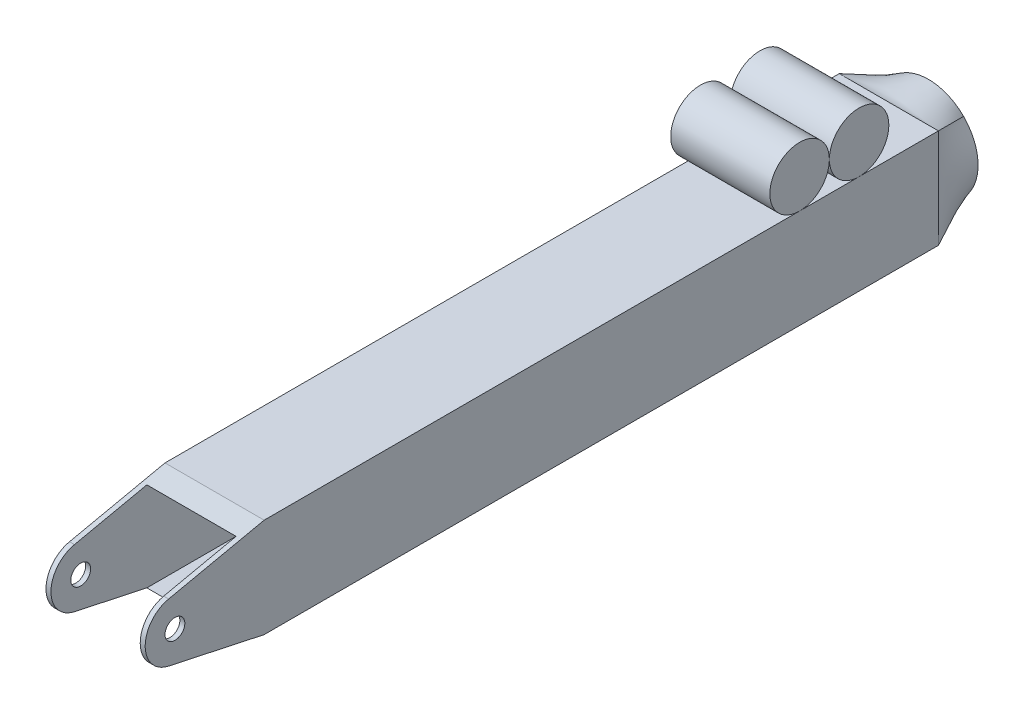
SolidWorks part; units mm, degrees
ref_plane "Front Plane" through (0, 0, 0) normal (0, 0, 1) x (1, 0, 0)
ref_plane "Top Plane" through (0, 0, 0) normal (0, 1, 0) x (1, 0, 0)
ref_plane "Right Plane" through (0, 0, 0) normal (1, 0, 0) x (0, 0, -1)
sketch "Sketch1" plane through (0, 0, 0) normal (0, 0, 1) x (1, 0, 0)
  line L0 (-28.575, 28.575) -> (28.575, 28.575)
  line L1 (-31.75, -31.75) -> (31.75, -31.75)
  line L2 (-31.75, -31.75) -> (-31.75, 31.75)
  line L3 (-31.75, 31.75) -> (31.75, 31.75)
  line L4 (31.75, -31.75) -> (31.75, 31.75)
  line L5 (-31.75, -31.75) -> (31.75, 31.75) construction
  line L6 (-31.75, 31.75) -> (31.75, -31.75) construction
  line L7 (28.575, -28.575) -> (28.575, 28.575)
  line L8 (-28.575, -28.575) -> (28.575, -28.575)
  line L9 (-28.575, -28.575) -> (-28.575, 28.575)
  point P0 (0, 0)
  dimension "D1" = 63.5
  dimension "D2" = 3.175
extrude "Boss-Extrude1" add sketch "Sketch1" along normal blind 508 from offset 25.4
sketch "Sketch2" plane through (0, 0, 0) normal (0, 0, 1) x (1, 0, 0)
  circle A0 centre (0, 0) radius 31.75
  dimension "D1" = 63.5
sketch "Sketch3" plane through (0, 0, 25.4) normal (0, 0, -1) x (-1, 0, 0)
  line L0 (31.75, 31.75) -> (31.75, -31.75) construction
  line L1 (31.75, -31.75) -> (-31.75, -31.75) construction
  line L2 (-31.75, -31.75) -> (-31.75, 31.75) construction
  line L3 (-31.75, 31.75) -> (31.75, 31.75) construction
  line L4 (31.75, 31.75) -> (31.75, -31.75)
  line L5 (31.75, -31.75) -> (-31.75, -31.75)
  line L6 (-31.75, -31.75) -> (-31.75, 31.75)
  line L7 (-31.75, 31.75) -> (31.75, 31.75)
loft "Loft1" add profiles "Sketch2", "Sketch3"
sketch "Sketch4" plane through (31.75, 0, 0) normal (1, 0, 0) x (0, 0, -1)
  line L0 (-533.4, -31.75) -> (-533.4, 31.75) construction
  line L1 (-518.3477, 18.6258) -> (-457.2, 31.75)
  line L2 (-533.4, 31.75) -> (-25.4, 31.75) construction
  line L3 (-518.3477, -18.6258) -> (-457.2, -31.75)
  line L4 (-533.4, -31.75) -> (-25.4, -31.75) construction
  line L5 (-457.2, -31.75) -> (-533.4, -31.75)
  line L6 (-533.4, -31.75) -> (-533.4, 0)
  line L7 (-533.4, 0) -> (-533.4, 31.75)
  line L8 (-533.4, 31.75) -> (-457.2, 31.75)
  arc A0 (-518.3477, 18.6258) -> (-518.3477, -18.6258) centre (-514.35, 0) ccw
  circle A1 centre (-514.35, 0) radius 6.35
  arc A2 (-518.3477, -18.6258) -> (-518.3477, 18.6258) centre (-514.35, 0) ccw construction
  line M6 (-25.4, 31.75) -> (-533.4, 31.75)
  line M7 (-533.4, 31.75) -> (-533.4, -31.75)
  line M8 (-533.4, -31.75) -> (-25.4, -31.75)
  dimension "D1" = 12.7
  dimension "D2" = 38.1
  dimension "D3" = 76.2
extrude "Cut-Extrude1" cut sketch "Sketch4" against normal through all contours A0 L3 M7 M8 | A0 L1 M6 M7 | A1
sketch "Sketch5" plane through (31.75, 0, 0) normal (1, 0, 0) x (0, 0, -1)
  line L0 (-457.2, 31.75) -> (-25.4, 31.75) construction
  circle A0 centre (-76.2, 50.8) radius 19.05
  circle A1 centre (-114.3, 50.8) radius 19.05
  line M7 (-25.4, -31.75) -> (-25.4, 31.75)
  dimension "D1" = 38.1
  dimension "D2" = 76.2
extrude "Boss-Extrude2" add sketch "Sketch5" against normal up to surface (63.5 mm away) separate body contours A1 | A0 M7 up to face at (-31.75, 0, 508)
